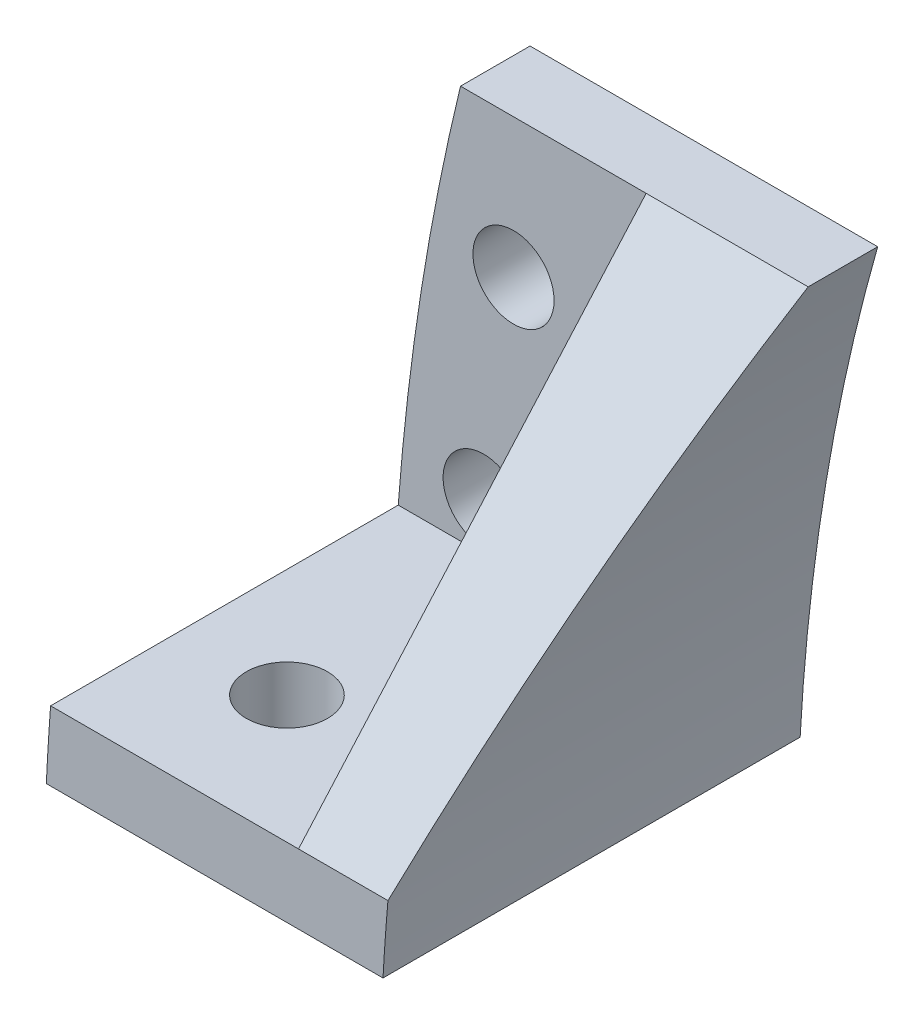
SolidWorks part; units mm, degrees
ref_plane "Front Plane" through (0, 0, 0) normal (0, 0, 1) x (1, 0, 0)
ref_plane "Top Plane" through (0, 0, 0) normal (0, 1, 0) x (1, 0, 0)
ref_plane "Right Plane" through (0, 0, 0) normal (1, 0, 0) x (0, 0, -1)
sketch "Sketch1" plane through (0, 0, 0) normal (0, 0, 1) x (1, 0, 0)
  line L0 (106, 0) -> (0, 0) construction
  line L1 (0.118, 5) -> (14.6451, 5)
  line L2 (2.9903, 25) -> (17.9903, 25)
  circle A0 centre (106, 0) radius 106 construction
  circle A1 centre (106, 0) radius 102.5 construction
  arc A2 (0.118, 5) -> (2.9903, 25) centre (106, 0) cw
  arc A3 (14.6451, 5) -> (17.9903, 25) centre (106, 0) cw
  circle A4 centre (3.989, 10) radius 1.75
  circle A5 centre (5.2764, 19) radius 1.75
  dimension "D1" = 212
  dimension "D2" = 205
  dimension "D8" = 3.5
  dimension "D3" = 5
  dimension "D4" = 20
  dimension "D5" = 15
  dimension "D6" = 10
  dimension "D7" = 9
extrude "Boss-Extrude1" add sketch "Sketch1" along normal blind 3
sketch "Sketch2" plane through (0, 0, 3) normal (0, 0, 1) x (1, 0, 0)
  line L0 (0.118, 5) -> (14.6451, 5) construction
  line L1 (0.118, 5) -> (14.6451, 5)
  line L2 (0.3023, 8) -> (14.8589, 8)
  arc A0 (17.9903, 25) -> (14.6451, 5) centre (106, 0) ccw construction
  arc A1 (2.9903, 25) -> (0.118, 5) centre (106, 0) ccw construction
  arc A2 (14.8589, 8) -> (14.6451, 5) centre (106, 0) ccw
  arc A3 (0.3023, 8) -> (0.118, 5) centre (106, 0) ccw
  dimension "D1" = 3
extrude "Boss-Extrude2" add sketch "Sketch2" along normal blind 15
ref_plane "Plane1" through (11, 0, 0) normal (1, 0, 0) x (0, 0, -1)
sketch "Sketch3" plane through (11, 0, 0) normal (1, 0, 0) x (0, 0, -1)
  line L0 (-18, 8) -> (-3, 25)
  line L1 (-3, 25) -> (-3, 8)
  line L2 (-3, 8) -> (-18, 8)
extrude "Boss-Extrude3" add sketch "Sketch3" along normal up to surface (3.8589 mm away)
sketch "Sketch4" plane through (0, 8, 0) normal (0, 1, 0) x (1, 0, 0)
  circle A0 centre (5, -12.5) radius 1.75
  dimension "D3" = 3.5
  dimension "D1" = 12.5
  dimension "D2" = 5
extrude "Cut-Extrude1" cut sketch "Sketch4" against normal through all
